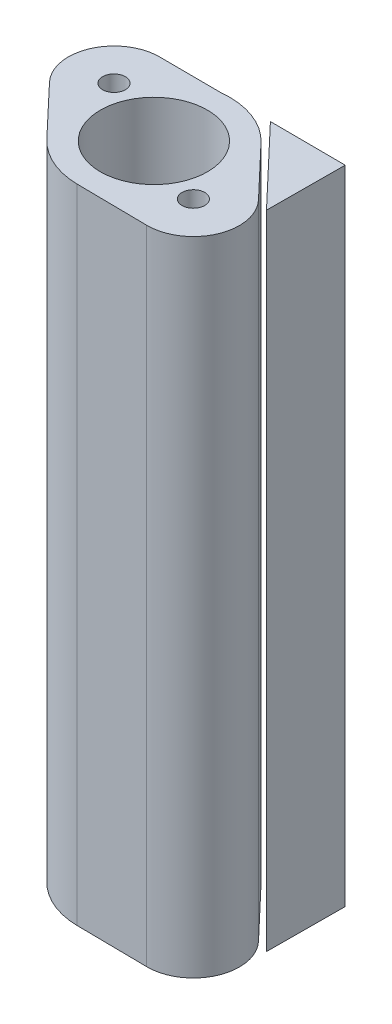
SolidWorks part; units mm, degrees
ref_plane "Alzado" through (0, 0, 0) normal (0, 0, 1) x (1, 0, 0)
ref_plane "Planta" through (0, 0, 0) normal (0, 1, 0) x (1, 0, 0)
ref_plane "Vista lateral" through (0, 0, 0) normal (1, 0, 0) x (0, 0, -1)
sketch "Croquis1" plane through (0, 0, 0) normal (0, 1, 0) x (1, 0, 0)
  line L5 (-15.9672, 0) -> (27.2389, 0) construction
  line L6 (4.5025, -6.4299) -> (7.7475, -9.8452)
  line L7 (0.2773, -4.8807) -> (-3.7666, -4.8594)
  line L8 (-6.079, -10.0131) -> (-2.8589, -13.4131)
  line L9 (5.4737, -15.0545) -> (0.763, -14.9973)
  circle A0 centre (0.8246, -9.9244) radius 3.584
  circle A1 centre (-3.8612, -7.9126) radius 0.7617
  circle A2 centre (5.5112, -11.97) radius 0.7617
  arc A3 (-3.7666, -4.8594) -> (-6.079, -10.0131) centre (-3.8612, -7.9126) ccw
  arc A4 (5.4737, -15.0545) -> (7.7475, -9.8452) centre (5.5112, -11.97) ccw
  arc A5 (4.5025, -6.4299) -> (0.2773, -4.8807) centre (0.8246, -9.9244) ccw
  arc A7 (-2.8589, -13.4131) -> (0.763, -14.9973) centre (0.8246, -9.9244) ccw
  point P6 (0.8246, -9.9244)
  point P7 (8.1812, -2.9347)
  point P10 (0.8246, -9.9244)
  point P13 (-3.8612, -7.9126)
  point P16 (-0.2587, 0.1653)
  point P34 (9.9381, -20.1835)
  point P35 (10.014, -13.9354)
  point P36 (14.5439, -9.6314)
extrude "Main" add sketch "Croquis1" against normal blind 50
ref_plane " Plano base" through (-0.0257, 0, 4.8791) normal (0.0053, 0, -1) x (-1, 0, -0.0053)
sketch "Croquis9" plane through (-0.0257, 0, 4.8791) normal (0.0053, 0, -1) x (-1, 0, -0.0053)
  line L1 (-7.7993, 0) -> (-4.5363, 0) construction
  line L2 (-7.7993, -50) -> (-4.5363, -50) construction
  line L3 (-3.4961, -50) -> (-3.4961, 0)
  line L4 (-8.659, 0) -> (-3.4961, 0)
  line L5 (-8.659, -50) -> (-3.4961, -50)
  line L6 (-8.659, 0) -> (-8.659, -50)
  line L7 (-8.659, 0) -> (-8.659, -50) construction
  line L8 (-4.4861, -49) -> (-4.4861, -43.7341)
  line L9 (-7.659, -1) -> (-4.4861, -1)
  line L10 (-7.659, -1) -> (-7.659, -6.5688)
  line L11 (-7.659, -49) -> (-4.4861, -49)
  line L12 (-7.659, -6.5688) -> (-4.4861, -6.5688)
  line L13 (-7.659, -8.2515) -> (-4.4861, -8.2515)
  line L14 (-7.659, -23.6419) -> (-4.4861, -23.6419)
  line L15 (-7.659, -25.2786) -> (-4.4861, -25.2786)
  line L16 (-7.659, -41.6884) -> (-4.4861, -41.6884)
  line L17 (-7.659, -43.7341) -> (-4.4861, -43.7341)
  line L18 (-7.659, -8.2515) -> (-7.659, -14.6298)
  line L19 (-4.4861, -6.5688) -> (-4.4861, -1)
  line L20 (-7.659, -14.6298) -> (-4.4861, -14.6298)
  line L21 (-7.659, -25.2786) -> (-7.659, -32.5358)
  line L22 (-7.659, -15.9467) -> (-4.4861, -15.9467)
  line L23 (-4.4861, -23.6419) -> (-4.4861, -15.9467)
  line L24 (-4.4861, -41.6884) -> (-4.4861, -33.8271)
  line L25 (-7.659, -43.7341) -> (-7.659, -49)
  line L26 (-7.659, -32.5358) -> (-4.4861, -32.5358)
  line L27 (-7.659, -33.8271) -> (-4.4861, -33.8271)
  line L28 (-4.4861, -32.5358) -> (-4.4861, -25.2786)
  line L29 (-7.659, -33.8271) -> (-7.659, -41.6884)
  line L30 (-7.659, -15.9467) -> (-7.659, -23.6419)
  line L31 (-4.4861, -14.6298) -> (-4.4861, -8.2515)
extrude "Soporte impresión" add sketch "Croquis9" against normal offset from surface (5.2429 mm away) 0.4 separate body
sketch "Croquis10" plane through (0, 0, 0) normal (0, 0, 1) x (1, 0, 0)
  line L0 (-10.8202, 0) -> (15.3163, 0) construction
  line L1 (-11.6463, -7) -> (16.3678, -7) construction
  line L3 (-7.6554, 0.9985) -> (9.2752, 0.9985)
  line L4 (-7.6554, 0.9985) -> (-7.6554, -7)
  line L5 (-7.6554, -7) -> (9.2752, -7)
  line L6 (9.2752, 0.9985) -> (9.2752, -7)
  dimension "D1" = 7
extrude "Ajuste de longitud" cut sketch "Croquis10" along normal blind 20
